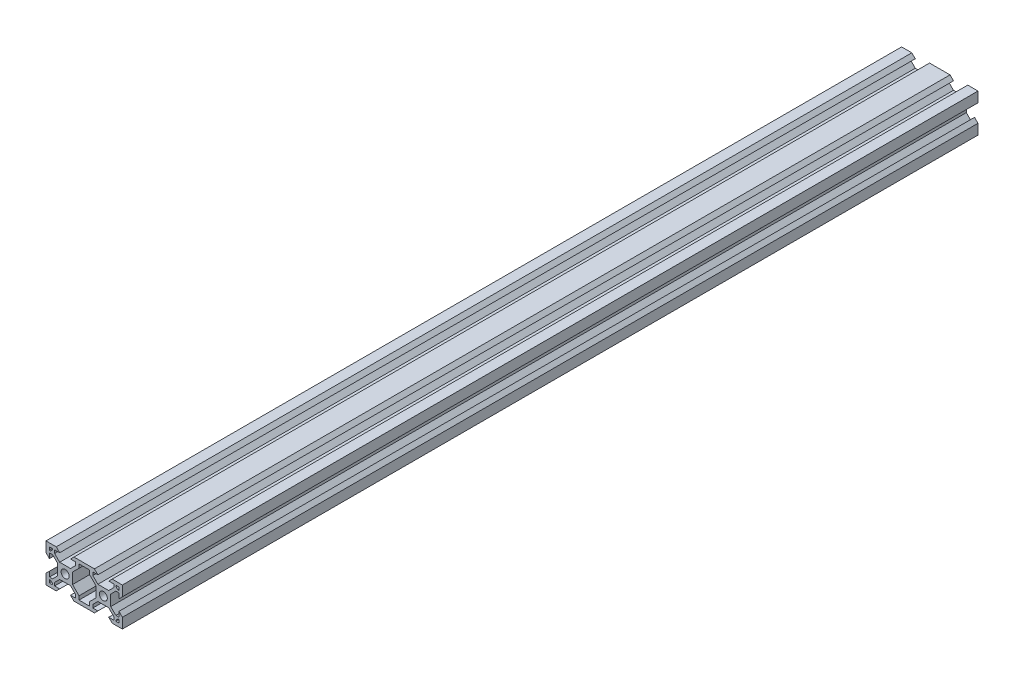
SolidWorks part; units mm, degrees
ref_plane "Front Plane" through (0, 0, 0) normal (0, 0, 1) x (1, 0, 0)
ref_plane "Top Plane" through (0, 0, 0) normal (0, 1, 0) x (1, 0, 0)
ref_plane "Right Plane" through (0, 0, 0) normal (1, 0, 0) x (0, 0, -1)
sketch "Sketch1" plane through (0, 0, 0) normal (0, 0, 1) x (1, 0, 0)
  line L0 (0, 0) -> (0, 5.36)
  line L1 (0, 20) -> (5.36, 20)
  line L3 (20, 0) -> (14.64, 0)
  line L4 (0, 10) -> (20, 10) construction
  line L5 (5.36, 0) -> (0, 0)
  line L6 (4.5007, 18.2) -> (7.16, 18.2)
  line L7 (17.3007, 3.76) -> (17.3007, 1.8)
  line L8 (15.4993, 1.8) -> (12.84, 1.8)
  line L9 (20, 0) -> (0, 0) construction
  line L10 (7.16, 1.8) -> (4.5007, 1.8)
  line L11 (15.4993, 3.44) -> (12.84, 6.0993)
  line L12 (4.5007, 16.56) -> (7.16, 13.9007)
  line L13 (13.9007, 12.84) -> (13.9007, 7.16)
  line L14 (12.84, 13.9007) -> (7.16, 13.9007)
  line L15 (6.0993, 12.84) -> (6.0993, 7.16)
  line L16 (7.16, 6.0993) -> (12.84, 6.0993)
  line L17 (4.5007, 16.56) -> (4.5007, 18.2)
  line L18 (3.44, 15.4993) -> (1.8, 15.4993)
  line L19 (4.5007, 3.44) -> (4.5007, 1.8)
  line L20 (3.44, 4.5007) -> (1.8, 4.5007)
  line L21 (15.4993, 3.44) -> (15.4993, 1.8)
  line L23 (17.3007, 1.8) -> (22.7007, 1.8)
  line L24 (15.4993, 16.56) -> (15.4993, 18.2)
  line L25 (7.16, 18.2) -> (5.36, 20)
  line L26 (12.84, 1.8) -> (14.64, 0)
  line L27 (7.16, 1.8) -> (5.36, 0)
  line L28 (12.84, 18.2) -> (14.64, 20)
  line L29 (1.8, 7.16) -> (0, 5.36)
  line L30 (1.8, 12.84) -> (0, 14.64)
  line L31 (22.7007, 1.8) -> (22.7007, 3.76)
  line L32 (17.3007, 16.24) -> (17.3007, 18.2)
  line L33 (17.3007, 18.2) -> (22.6993, 18.2)
  line L34 (22.6993, 18.2) -> (22.6993, 16.24)
  line L35 (38.2013, 12.8423) -> (40.001, 14.6427)
  line L36 (38.2024, 7.1623) -> (40.0028, 5.3627)
  line L37 (27.16, 18.2) -> (25.36, 20)
  line L38 (32.84, 1.8) -> (34.64, 0)
  line L39 (27.16, 1.8) -> (25.36, 0)
  line L40 (32.84, 18.2) -> (34.64, 20)
  line L41 (24.5013, 16.5597) -> (24.5009, 18.2)
  line L42 (1.8, 18.2) -> (3.4307, 18.2)
  line L43 (3.4307, 18.2) -> (3.4307, 17.63)
  line L44 (24.5038, 3.4397) -> (24.5041, 1.8)
  line L45 (36.5629, 4.5027) -> (38.2029, 4.503)
  line L46 (35.5025, 3.4418) -> (35.5028, 1.8)
  line L47 (36.5608, 15.5014) -> (38.2008, 15.5017)
  line L48 (35.4999, 16.5618) -> (35.4996, 18.2)
  line L49 (32.8426, 6.1006) -> (27.1626, 6.0995)
  line L50 (33.902, 12.8415) -> (33.9031, 7.1615)
  line L51 (27.1611, 13.9009) -> (32.8411, 13.902)
  line L52 (26.1007, 12.84) -> (26.1007, 7.16)
  line L53 (1.8, 4.5007) -> (1.8, 7.16)
  line L54 (24.5038, 3.4397) -> (27.1626, 6.0995)
  line L55 (35.5025, 3.4418) -> (32.8426, 6.1006)
  line L56 (36.5629, 4.5027) -> (33.9031, 7.1615)
  line L57 (24.5041, 1.8) -> (27.16, 1.8)
  line L58 (3.4307, 17.63) -> (2.37, 16.5693)
  line L59 (3.44, 4.5007) -> (6.0993, 7.16)
  line L60 (35.4996, 18.2) -> (32.84, 18.2)
  line L61 (20, 0) -> (25.36, 0)
  line L62 (39.9999, 20) -> (34.64, 20)
  line L63 (40.0038, 0) -> (40.0028, 5.3627)
  line L64 (1.8, 12.84) -> (1.8, 15.4993)
  line L65 (1.8, 1.8) -> (1.8, 18.2) construction
  line L66 (0, 14.64) -> (0, 20)
  line L67 (0, 0) -> (0, 20) construction
  line L68 (14.64, 20) -> (20, 20)
  line L69 (0, 20) -> (20, 20) construction
  line L70 (12.84, 18.2) -> (15.4993, 18.2)
  line L71 (1.8, 18.2) -> (18.2, 18.2) construction
  line L72 (25.36, 20) -> (20, 20)
  line L73 (27.16, 18.2) -> (24.5009, 18.2)
  line L74 (38.2013, 12.8423) -> (38.2008, 15.5017)
  line L75 (40.001, 14.6427) -> (39.9999, 20)
  line L76 (32.84, 1.8) -> (35.5028, 1.8)
  line L77 (34.64, 0) -> (40.0038, 0)
  line L78 (38.2029, 4.503) -> (38.2024, 7.1623)
  line L79 (35.4999, 16.5618) -> (32.8411, 13.902)
  line L80 (4.5007, 3.44) -> (7.16, 6.0993)
  line L81 (2.37, 16.5693) -> (1.8, 16.5693)
  line L82 (18.2, 1.8) -> (1.8, 1.8) construction
  line L83 (18.2, 18.2) -> (18.2, 1.8) construction
  line L84 (1.8, 16.5693) -> (1.8, 18.2)
  line L85 (20, 20) -> (20, 0) construction
  line L86 (1.8, 3.4307) -> (1.8, 1.8)
  line L87 (2.37, 3.4307) -> (1.8, 3.4307)
  line L88 (3.4307, 2.37) -> (2.37, 3.4307)
  line L89 (3.4307, 1.8) -> (3.4307, 2.37)
  line L90 (1.8, 1.8) -> (3.4307, 1.8)
  line L91 (13.9007, 7.16) -> (17.3007, 3.76)
  line L92 (20, 20) -> (20, -0.3542) construction
  line L93 (38.2, 1.8) -> (36.5693, 1.8)
  line L94 (36.5693, 1.8) -> (36.5693, 2.37)
  line L95 (36.5693, 2.37) -> (37.63, 3.4307)
  line L96 (37.63, 3.4307) -> (38.2, 3.4307)
  line L97 (38.2, 3.4307) -> (38.2, 1.8)
  line L98 (38.2, 16.5693) -> (38.2, 18.2)
  line L99 (37.63, 16.5693) -> (38.2, 16.5693)
  line L100 (36.5693, 17.63) -> (37.63, 16.5693)
  line L101 (36.5693, 18.2) -> (36.5693, 17.63)
  line L102 (38.2, 18.2) -> (36.5693, 18.2)
  line L103 (6.0993, 12.84) -> (3.44, 15.4993)
  line L104 (13.9007, 12.84) -> (17.3007, 16.24)
  line L105 (12.84, 13.9007) -> (15.4993, 16.56)
  line L106 (33.902, 12.8415) -> (36.5608, 15.5014)
  line L108 (27.1611, 13.9009) -> (24.5013, 16.5597)
  line L109 (26.1007, 12.84) -> (22.6993, 16.24)
  line L110 (26.1007, 7.16) -> (22.7007, 3.76)
  circle A0 centre (10, 10) radius 2.1
  circle A1 centre (30, 10) radius 2.1
  point P14 (17.3007, 3.76)
  point P81 (0, 0)
  point P82 (0, 0)
  point P112 (17.3007, 1.8)
  dimension "D3" = 4.2
  dimension "D1" = 20
  dimension "D2" = 20
  dimension "D5" = 5.4
  dimension "D7" = 1.07
  dimension "D8" = 45
  dimension "D9" = 1.5
  dimension "D10" = 4.5007
  dimension "D11" = 5.68
  dimension "D12" = 5.68
  dimension "D13" = 5.68
  dimension "D14" = 5.68
  dimension "D15" = 1.64
  dimension "D16" = 1.64
  dimension "D17" = 1.64
  dimension "D18" = 1.64
  dimension "D19" = 1.64
  dimension "D20" = 15.4993
  dimension "D21" = 1.07
  dimension "D22" = 1.64
  dimension "D23" = 45
  dimension "D24" = 45
  dimension "D25" = 1.5
  dimension "D26" = 45
  dimension "D27" = 45
  dimension "D28" = 45
  dimension "D4" = 1.8
extrude "Boss-Extrude1" add sketch "Sketch1" against normal blind 448
